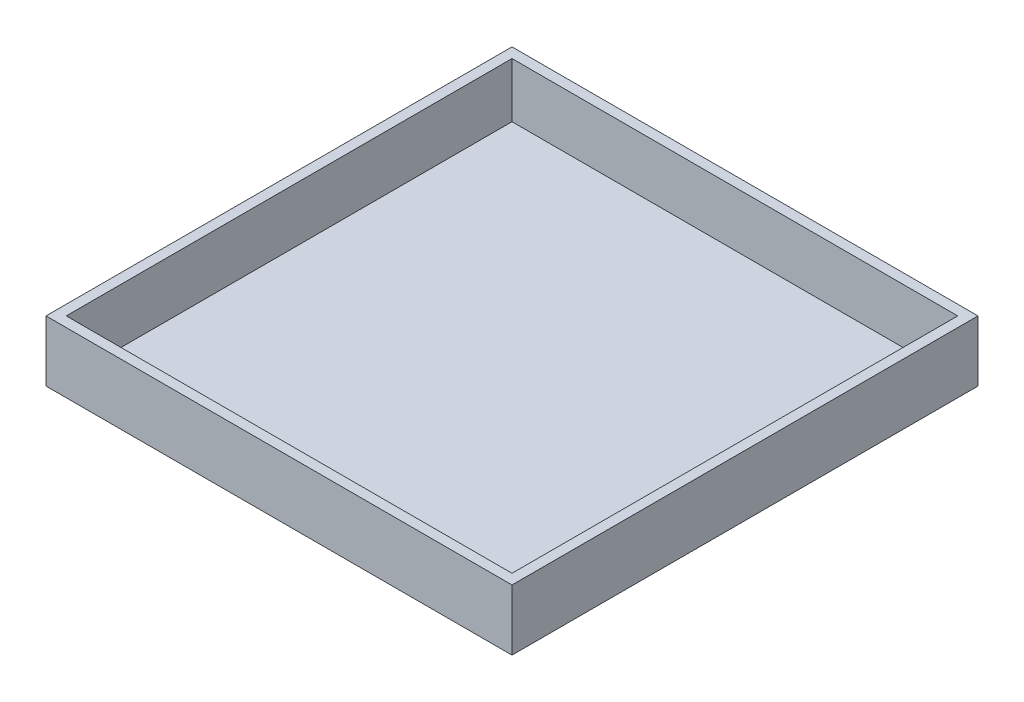
SolidWorks part; units mm, degrees
ref_plane "Спереди" through (0, 0, 0) normal (0, 0, 1) x (1, 0, 0)
ref_plane "Сверху" through (0, 0, 0) normal (0, 1, 0) x (1, 0, 0)
ref_plane "Справа" through (0, 0, 0) normal (1, 0, 0) x (0, 0, -1)
sketch "Эскиз1" plane through (0, 0, 0) normal (0, 1, 0) x (1, 0, 0)
  line L1 (-110, -110) -> (110, -110)
  line L2 (-110, -110) -> (-110, 110)
  line L3 (-110, 110) -> (110, 110)
  line L4 (110, -110) -> (110, 110)
  line L5 (-110, -110) -> (110, 110) construction
  line L6 (-110, 110) -> (110, -110) construction
  point P0 (0, 0)
  dimension "D1" = 220
extrude "Бобышка-Вытянуть1" add sketch "Эскиз1" along normal blind 3
sketch "Эскиз2" plane through (0, 0, 0) normal (0, 1, 0) x (1, 0, 0)
  line L1 (-110, -110) -> (110, -110)
  line L2 (-110, -110) -> (-110, 110)
  line L3 (-110, 110) -> (110, 110)
  line L4 (110, -110) -> (110, 110)
  line L5 (-110, -110) -> (110, 110) construction
  line L6 (-110, 110) -> (110, -110) construction
  line L7 (-115, -115) -> (115, -115)
  line L8 (-115, -115) -> (-115, 115)
  line L9 (-115, 115) -> (115, 115)
  line L10 (115, -115) -> (115, 115)
  line L11 (-115, -115) -> (115, 115) construction
  line L12 (-115, 115) -> (115, -115) construction
  point P0 (0, 0)
  point P5 (0, 0)
  dimension "D1" = 230
extrude "Бобышка-Вытянуть2" add sketch "Эскиз2" along normal blind 30
